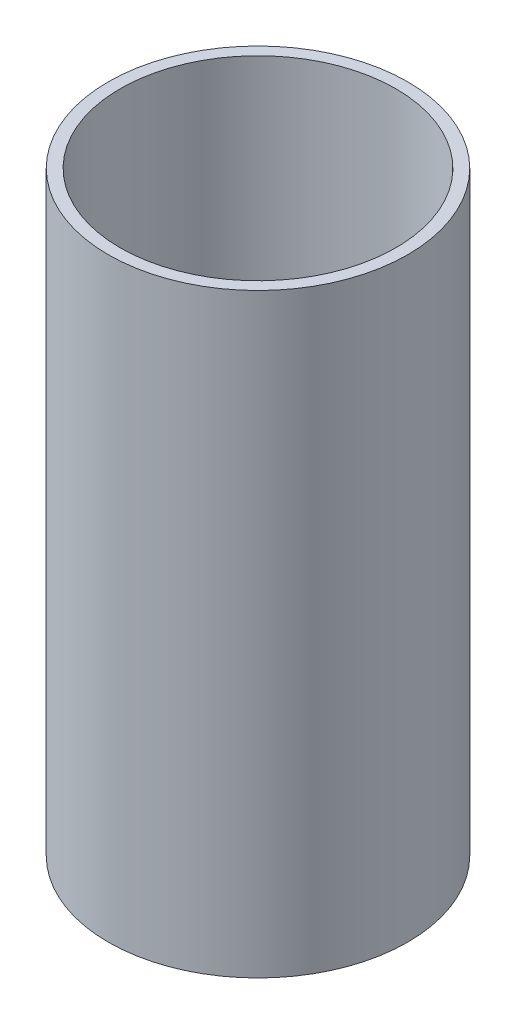
SolidWorks part; units mm, degrees
ref_plane "Front Plane" through (0, 0, 0) normal (0, 0, 1) x (1, 0, 0)
ref_plane "Top Plane" through (0, 0, 0) normal (0, 1, 0) x (1, 0, 0)
ref_plane "Right Plane" through (0, 0, 0) normal (1, 0, 0) x (0, 0, -1)
sketch "Sketch1" plane through (0, 0, 0) normal (0, 1, 0) x (1, 0, 0)
  circle A0 centre (0, 0) radius 25.15
  circle A1 centre (0, 0) radius 23.15
  dimension "D1" = 50.3
  dimension "D2" = 2
extrude "Boss-Extrude1" add sketch "Sketch1" along normal blind 100
sketch "Sketch2" plane through (0, 0, 0) normal (0, -1, 0) x (1, 0, 0)
  circle A0 centre (0, 0) radius 25.15
extrude "Boss-Extrude2" add sketch "Sketch2" against normal blind 3
